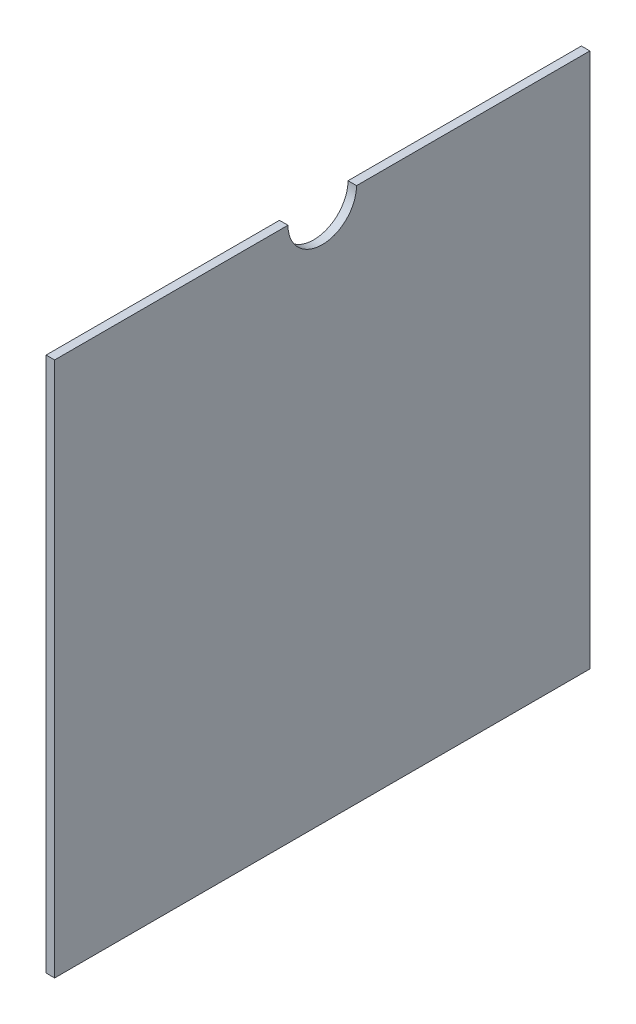
SolidWorks part; units mm, degrees
ref_plane "Front Plane" through (0, 0, 0) normal (0, 0, 1) x (1, 0, 0)
ref_plane "Top Plane" through (0, 0, 0) normal (0, 1, 0) x (1, 0, 0)
ref_plane "Right Plane" through (0, 0, 0) normal (1, 0, 0) x (0, 0, -1)
sketch "Sketch1" plane through (0, 0, 0) normal (1, 0, 0) x (0, 0, -1)
  line L5 (0, 199.9996) -> (87.2998, 199.9996)
  line L6 (0, 0) -> (199.9996, 0)
  line L7 (0, 0) -> (0, 199.9996)
  line L9 (199.9996, 0) -> (199.9996, 199.9996)
  line L11 (112.6998, 199.9996) -> (199.9996, 199.9996)
  arc A3 (87.2998, 199.9996) -> (112.6998, 199.9996) centre (99.9998, 199.9996) ccw
  point P5 (0, 0)
  dimension "D2" = 25.4
  dimension "D1" = 199.9996
extrude "Boss-Extrude1" add sketch "Sketch1" along normal blind 3.175
sketch "Sketch2" plane through (3.175, 0, 0) normal (1, 0, 0) x (0, 0, -1)
  line L0 (199.9996, 199.9996) -> (112.6998, 199.9996) construction
  line L1 (87.2998, 199.9996) -> (0, 199.9996) construction
  line L2 (0, 199.9996) -> (0, 0) construction
  line L3 (0, 0) -> (199.9996, 0) construction
  line L4 (199.9996, 0) -> (199.9996, 199.9996) construction
  line L5 (199.9996, 199.9996) -> (112.6998, 199.9996)
  line L6 (87.2998, 199.9996) -> (0, 199.9996)
  line L7 (0, 199.9996) -> (0, 0)
  line L8 (0, 0) -> (199.9996, 0)
  line L9 (199.9996, 0) -> (199.9996, 199.9996)
  line L10 (199.898, 199.898) -> (112.801, 199.898)
  line L11 (87.1986, 199.898) -> (0.1016, 199.898)
  line L12 (0.1016, 199.898) -> (0.1016, 0.1016)
  line L13 (0.1016, 0.1016) -> (199.898, 0.1016)
  line L14 (199.898, 0.1016) -> (199.898, 199.898)
  arc A0 (87.2998, 199.9996) -> (112.6998, 199.9996) centre (99.9998, 199.9996) ccw construction
  arc A1 (87.2998, 199.9996) -> (112.6998, 199.9996) centre (99.9998, 199.9996) ccw
  arc A2 (87.1986, 199.898) -> (112.801, 199.898) centre (99.9998, 199.9996) ccw
  dimension "D1" = 0.1016
extrude "Cut-Extrude1" cut sketch "Sketch2" against normal blind 3.175
